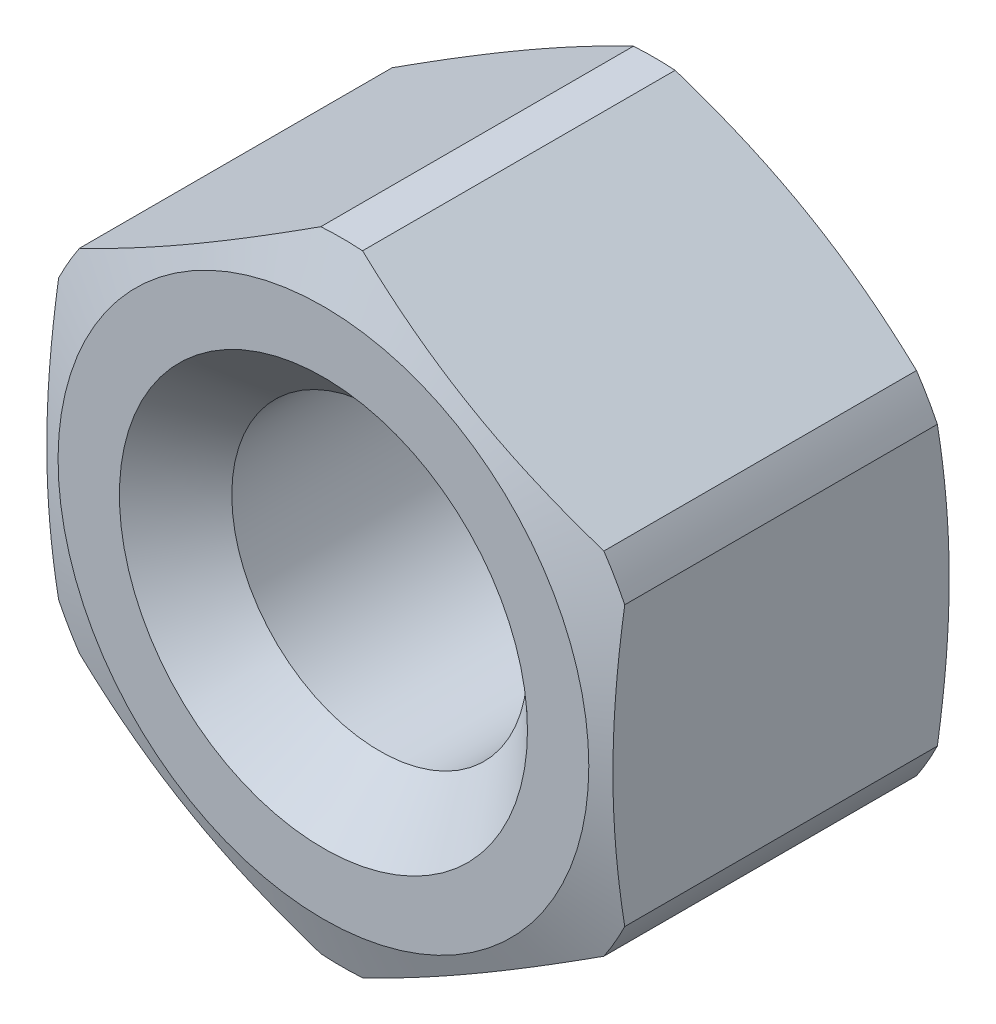
SolidWorks part; units mm, degrees
material "AISI 1020"
ref_plane "Спереди" through (0, 0, 0) normal (0, 0, 1) x (1, 0, 0)
ref_plane "Сверху" through (0, 0, 0) normal (0, 1, 0) x (1, 0, 0)
ref_plane "Справа" through (0, 0, 0) normal (1, 0, 0) x (0, 0, -1)
sketch "Эскиз1" plane through (0, 0, 0) normal (1, 0, 0) x (0, 0, -1)
  line L0 (-152.7402, 0) -> (7484.2692, 0) construction
  line L1 (-5.0179, 6.2679) -> (5.0179, 6.2679)
  line L5 (6.6266, 13.375) -> (-6.6266, 13.375)
  line L6 (-6.6266, 13.375) -> (-7.4, 11.25)
  line L7 (-7.4, 11.25) -> (-7.4, 8.65)
  line L8 (-7.4, 8.65) -> (-5.0179, 6.2679)
  line L9 (0, -152.7402) -> (0, 7484.2692) construction
  line L10 (0, 8) -> (0, -8) construction
  line L11 (-1, 8) -> (1, 8) construction
  line L12 (1, 8) -> (0, 6.2679) construction
  line L13 (0, 6.2679) -> (-1, 8) construction
  line L14 (6.6266, 13.375) -> (7.4, 11.25)
  line L15 (7.4, 11.25) -> (7.4, 8.65)
  line L16 (7.4, 8.65) -> (5.0179, 6.2679)
  point P8 (0, 0)
  point P16 (0, 8)
  point P20 (0, 13.375)
  point P23 (0, 6.2679)
  dimension "D1" = 20
  dimension "_e" = 26.75
  dimension "_dw" = 22.5
  dimension "D2" = 45
  dimension "_da" = 17.3
  dimension "_D" = 16
  dimension "_pa" = 2
  dimension "_m" = 14.8
revolve "Повернуть1" add sketch "Эскиз1" angle 360 about L0
sketch "Эскиз2" plane through (0, 0, 7.4) normal (0, 0, 1) x (1, 0, 0)
  line L1 (0, -13.8564) -> (12, -6.9282)
  line L2 (12, -6.9282) -> (12, 6.9282)
  line L3 (12, 6.9282) -> (0, 13.8564)
  line L4 (0, 13.8564) -> (-12, 6.9282)
  line L5 (-12, 6.9282) -> (-12, -6.9282)
  line L6 (-12, -6.9282) -> (0, -13.8564)
  circle A0 centre (0, 0) radius 12 construction
  dimension "_S" = 24
extrude "Вырез-Вытянуть1" cut sketch "Эскиз2" against normal through all flip side to cut
